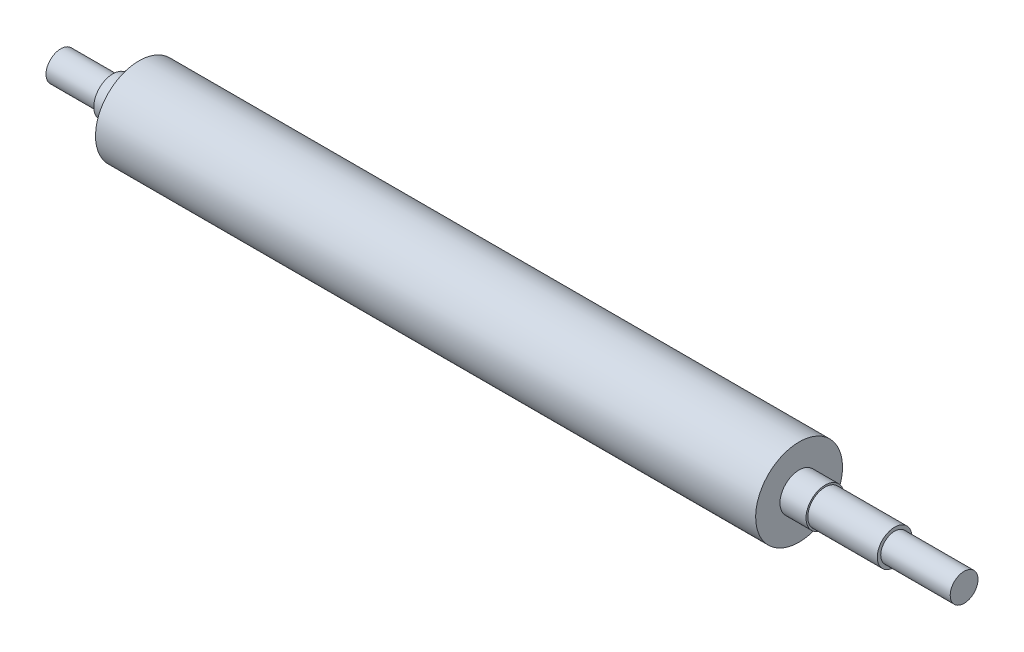
SolidWorks part; units mm, degrees
ref_plane "前视基准面" through (0, 0, 0) normal (0, 0, 1) x (1, 0, 0)
ref_plane "上视基准面" through (0, 0, 0) normal (0, 1, 0) x (1, 0, 0)
ref_plane "右视基准面" through (0, 0, 0) normal (1, 0, 0) x (0, 0, -1)
sketch "草图1" plane through (0, 0, 0) normal (0, 0, 1) x (1, 0, 0)
  line L0 (-230.7094, 0) -> (459.7941, 0) construction
  line L1 (0, 215.5466) -> (0, -189.8195) construction
  line L2 (-190, 25) -> (190, 25)
  line L6 (-235, 8.5) -> (-235, 0)
  line L7 (-205, 8.5) -> (-235, 8.5)
  line L8 (-190, 25) -> (-190, 11)
  line L9 (-235, 0) -> (285, 0)
  line L10 (-205, 8.5) -> (-205, 11)
  line L11 (-205, 11) -> (-190, 11)
  line L14 (205, 10) -> (205, 11)
  line L15 (205, 11) -> (190, 11)
  line L16 (190, 25) -> (190, 11)
  line L17 (205, 10) -> (245, 10)
  line L20 (245, 10) -> (245, 8)
  line L21 (245, 8) -> (285, 8)
  line L22 (285, 8) -> (285, 0)
  point P17 (0, 25)
  dimension "D1" = 11
  dimension "D2" = 8.5
  dimension "D3" = 25
  dimension "D4" = 380
  dimension "D5" = 30
  dimension "D6" = 15
  dimension "D7" = 15
  dimension "D8" = 40
  dimension "D9" = 8
  dimension "D10" = 10
  dimension "D11" = 40
revolve "旋转1" add sketch "草图1" angle 360 about L9
ref_plane "基准面1" through (0, -8, 0) normal (0, -1, 0) x (-1, 0, 0)
sketch "草图3" plane through (0, -8, 0) normal (0, -1, 0) x (-1, 0, 0)
  line L0 (-280, 0) -> (-250, 0) construction
  line L1 (-280, 3) -> (-250, 3)
  line L2 (-280, -3) -> (-250, -3)
  line L4 (-245, 10) -> (-245, -10) construction
  line L5 (-205, 10) -> (-245, 10) construction
  line L7 (-285, 8) -> (-285, -8) construction
  arc A0 (-280, 3) -> (-280, -3) centre (-280, 0) ccw
  arc A1 (-250, -3) -> (-250, 3) centre (-250, 0) ccw
  point P2 (-265, 0)
  dimension "D1" = 10
  dimension "D2" = 5
  dimension "D3" = 5
  dimension "D4" = 6
extrude "切除-拉伸1" cut sketch "草图3" against normal blind 3.5 contours L2 A1 L1 A0
